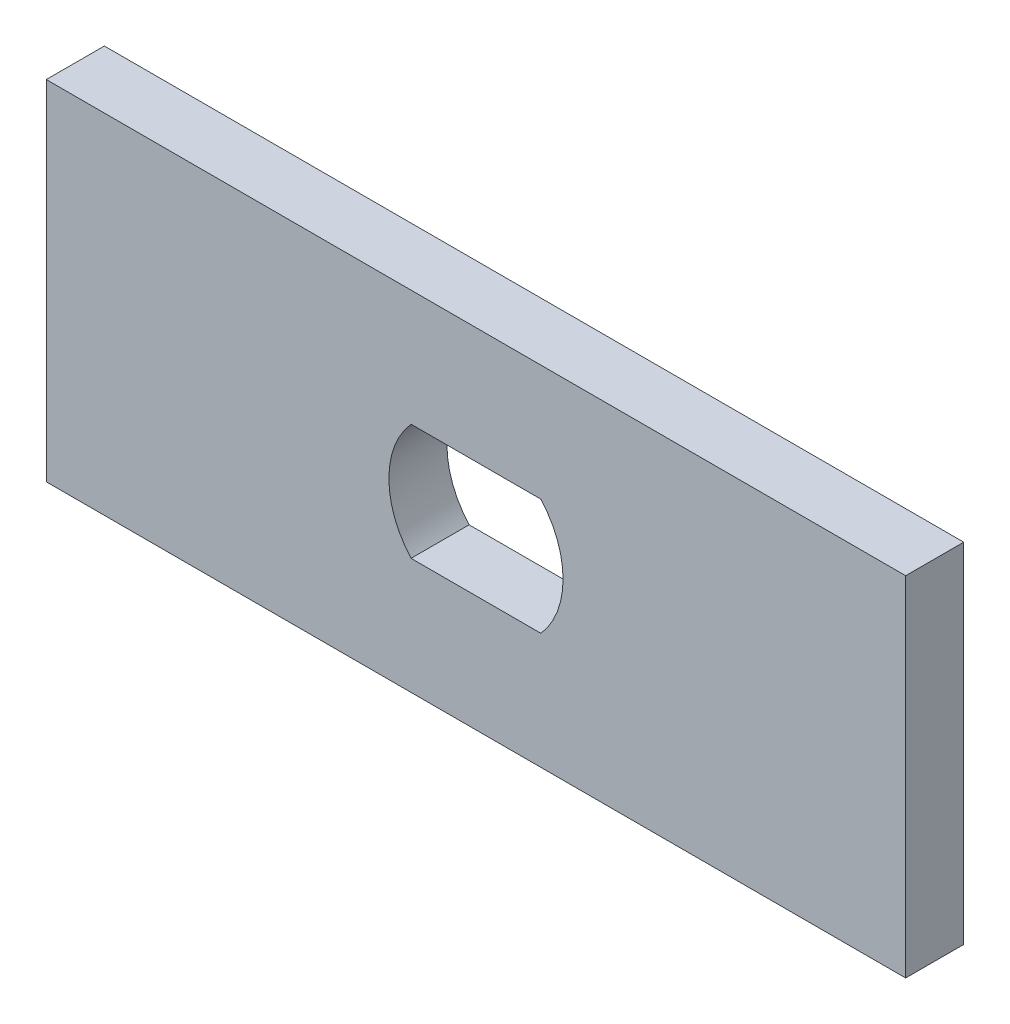
SolidWorks part; units mm, degrees
material "6061-T6 (SS)"
ref_plane "Front Plane" through (0, 0, 0) normal (0, 0, 1) x (1, 0, 0)
ref_plane "Top Plane" through (0, 0, 0) normal (0, 1, 0) x (1, 0, 0)
ref_plane "Right Plane" through (0, 0, 0) normal (1, 0, 0) x (0, 0, -1)
sketch "Sketch1" plane through (0, 0, 0) normal (0, 0, 1) x (1, 0, 0)
  line L1 (-46.99, 19.05) -> (46.99, 19.05)
  line L2 (-46.99, 19.05) -> (-46.99, -19.05)
  line L3 (-46.99, -19.05) -> (46.99, -19.05)
  line L4 (46.99, 19.05) -> (46.99, -19.05)
  line L5 (-46.99, 19.05) -> (46.99, -19.05) construction
  line L6 (-46.99, -19.05) -> (46.99, 19.05) construction
  line L7 (-7.0995, -6.35) -> (7.0995, -6.35)
  line L9 (-7.0995, 6.35) -> (7.0995, 6.35)
  line L11 (-7.0995, -6.35) -> (7.0995, 6.35) construction
  line L12 (-7.0995, 6.35) -> (7.0995, -6.35) construction
  arc A0 (-7.0995, 6.35) -> (-7.0995, -6.35) centre (0, 0) ccw
  arc A1 (7.0995, -6.35) -> (7.0995, 6.35) centre (0, 0) ccw
  point P0 (0, 0)
  dimension "D3" = 19.05
  dimension "D1" = 93.98
  dimension "D2" = 38.1
  dimension "D4" = 12.7
extrude "Boss-Extrude1" add sketch "Sketch1" along normal blind 6.35
